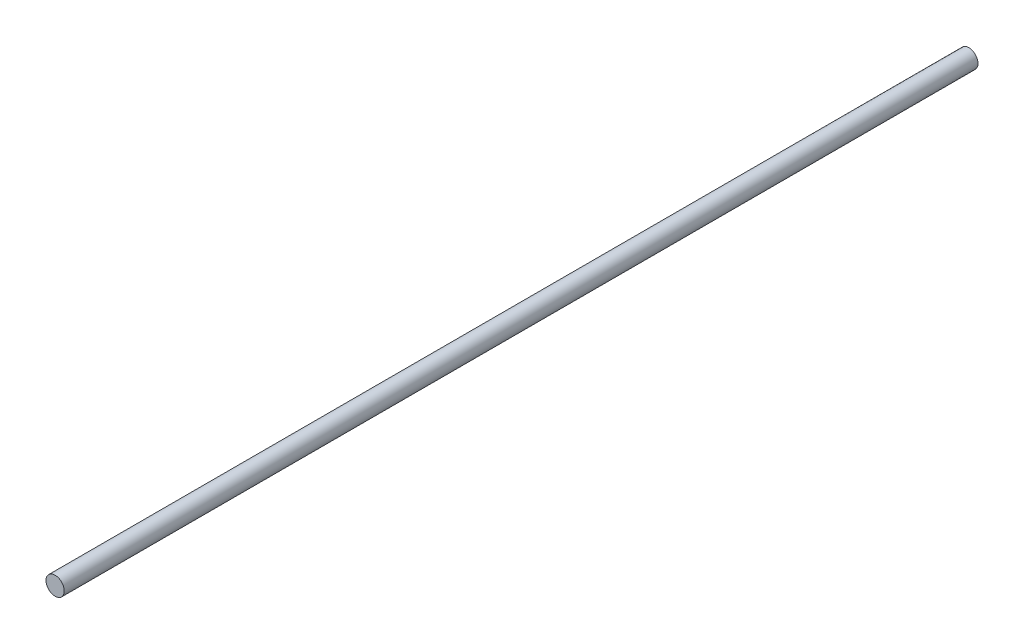
SolidWorks part; units mm, degrees
ref_plane "Front Plane" through (0, 0, 0) normal (0, 0, 1) x (1, 0, 0)
ref_plane "Top Plane" through (0, 0, 0) normal (0, 1, 0) x (1, 0, 0)
ref_plane "Right Plane" through (0, 0, 0) normal (1, 0, 0) x (0, 0, -1)
sketch "Sketch1" plane through (0, 0, 0) normal (0, 0, 1) x (1, 0, 0)
  circle A0 centre (0, 0) radius 4
  dimension "D1" = 8
extrude "Boss-Extrude1" add sketch "Sketch1" along normal blind 400
